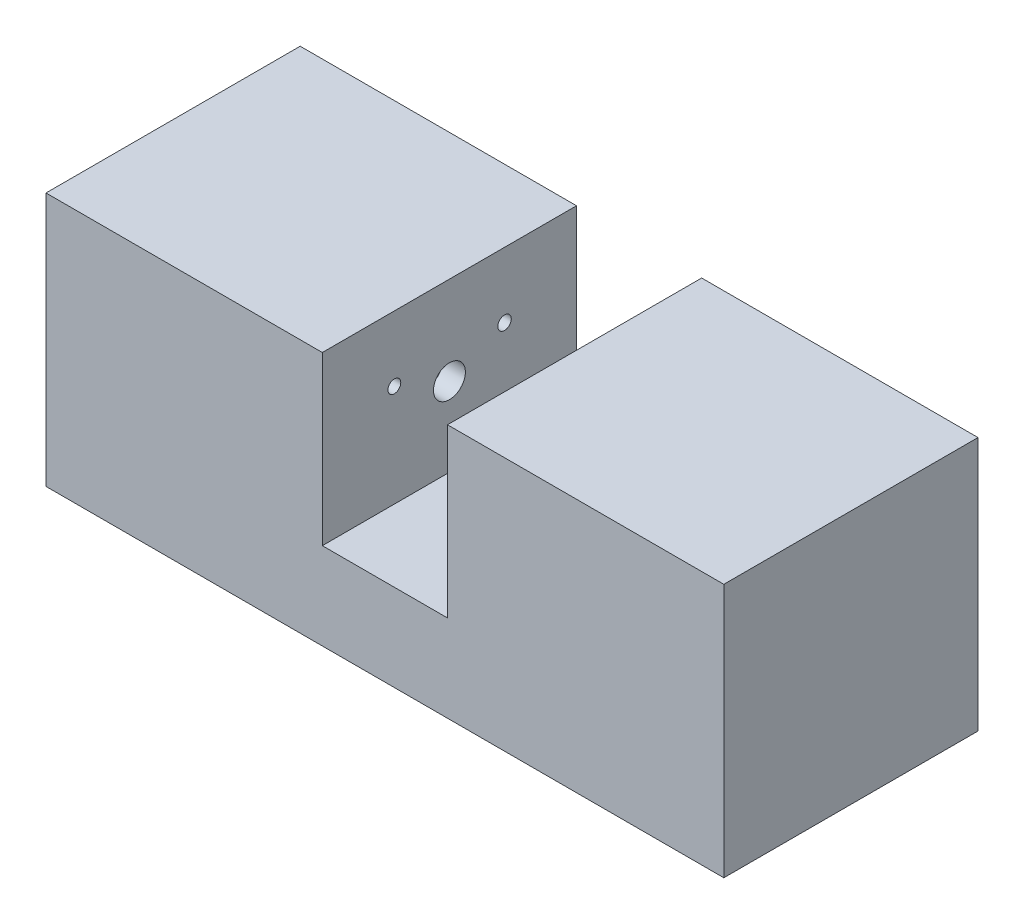
SolidWorks part; units mm, degrees
ref_plane "Front" through (0, 0, 0) normal (0, 0, 1) x (1, 0, 0)
ref_plane "Top" through (0, 0, 0) normal (0, 1, 0) x (1, 0, 0)
ref_plane "Right" through (0, 0, 0) normal (1, 0, 0) x (0, 0, -1)
sketch "Skica1" plane through (0, 0, 0) normal (1, 0, 0) x (0, 0, -1)
  line L1 (-15, 15) -> (15, 15)
  line L2 (-15, 15) -> (-15, -15)
  line L3 (-15, -15) -> (15, -15)
  line L4 (15, 15) -> (15, -15)
  line L5 (-15, 15) -> (15, -15) construction
  line L6 (-15, -15) -> (15, 15) construction
  point P0 (0, 0)
  dimension "D1" = 30
  dimension "D2" = 30
extrude "Přidat vysunutím1" add sketch "Skica1" along normal mid plane 80
sketch "Skica2" plane through (0, 0, -15) normal (0, 0, -1) x (-1, 0, 0)
  line L0 (0, 26.1707) -> (0, 0) construction
  line L1 (-7.3862, 57.0873) -> (7.3862, 57.0873)
  line L2 (-7.3862, 57.0873) -> (-7.3862, -4.7459)
  line L3 (-7.3862, -4.7459) -> (7.3862, -4.7459)
  line L4 (7.3862, 57.0873) -> (7.3862, -4.7459)
  line L5 (-7.3862, 57.0873) -> (7.3862, -4.7459) construction
  line L6 (-7.3862, -4.7459) -> (7.3862, 57.0873) construction
  point P0 (0, 26.1707)
  point P8 (0, 26.7988)
  point P9 (7.3862, -4.7459)
extrude "Odebrat vysunutím1" cut sketch "Skica2" against normal blind 180
sketch "Skica3" plane through (-40, 0, 0) normal (-1, 0, 0) x (0, 0, 1)
  line L1 (-11.3925, 12.9236) -> (11.3925, 12.9236)
  line L2 (-11.3925, 12.9236) -> (-11.3925, -12.9236)
  line L3 (-11.3925, -12.9236) -> (11.3925, -12.9236)
  line L4 (11.3925, 12.9236) -> (11.3925, -12.9236)
  line L5 (-11.3925, 12.9236) -> (11.3925, -12.9236) construction
  line L6 (-11.3925, -12.9236) -> (11.3925, 12.9236) construction
  point P0 (0, 0)
  point P6 (-11.3925, 12.9236)
extrude "Odebrat vysunutím2" cut sketch "Skica3" against normal blind 30
sketch "Skica4" plane through (-7.3862, 0, 0) normal (1, 0, 0) x (0, 0, -1)
  circle A4 centre (6.506, 7.2922) radius 0.7949
  circle A5 centre (-6.5019, 7.2922) radius 0.7588
  circle A6 centre (-6.2851, -9.6543) radius 1.0535
  circle A7 centre (6.506, -9.8711) radius 0.9756
extrude "Odebrat vysunutím3" cut sketch "Skica4" against normal blind 60
sketch "Skica5" plane through (-10, 0, 0) normal (-1, 0, 0) x (0, 0, 1)
  circle A0 centre (0, 4.5649) radius 1.8862
  point P2 (0, 4.5649)
extrude "Odebrat vysunutím4" cut sketch "Skica5" against normal blind 30
sketch "Skica6" plane through (0, 0, -15) normal (0, 0, -1) x (-1, 0, 0)
  line L0 (-40, -15) -> (-40, 15) construction
  line L1 (-40, 15) -> (-7.3862, 15) construction
  circle A0 centre (-30, 3) radius 5
  circle A2 centre (-30, 3) radius 4
  point P2 (-24.7984, 3.9381)
  dimension "D1" = 10
  dimension "D2" = 8
  dimension "D3" = 10
  dimension "D4" = 12
extrude "Přidat vysunutím2" add sketch "Skica6" along normal blind 5
mirror "Zrcadlit1" about plane through (0, 0, 0) normal (1, 0, 0) of "Přidat vysunutím2"
